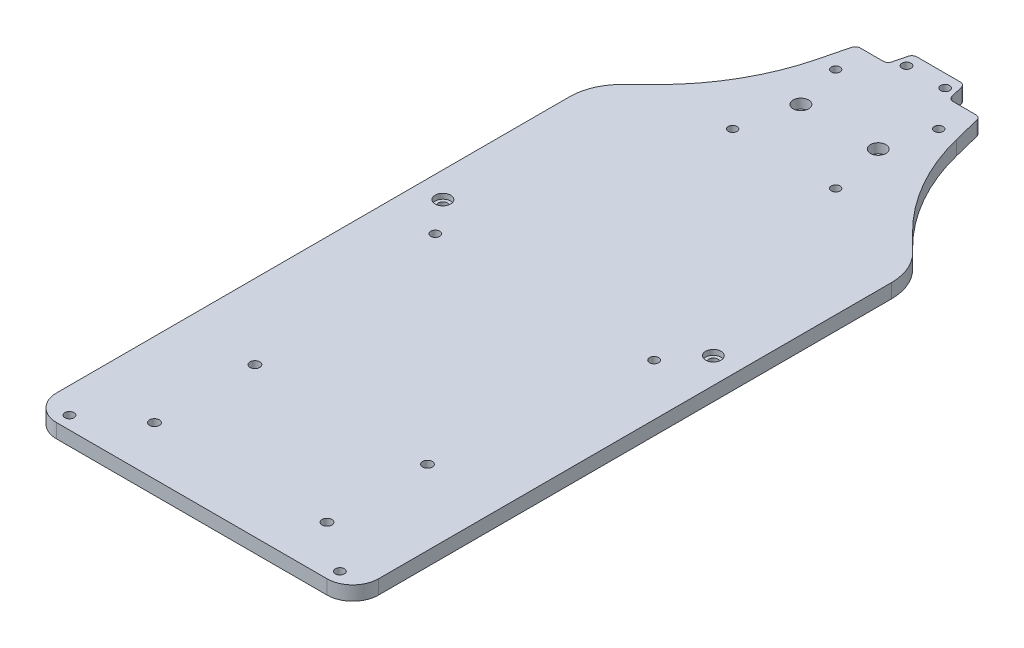
SolidWorks part; units mm, degrees
ref_plane "정면" through (0, 0, 0) normal (0, 0, 1) x (1, 0, 0)
ref_plane "윗면" through (0, 0, 0) normal (0, 1, 0) x (1, 0, 0)
ref_plane "우측면" through (0, 0, 0) normal (1, 0, 0) x (0, 0, -1)
sketch "스케치1" plane through (0, 0, 0) normal (0, 1, 0) x (1, 0, 0)
  line L0 (-857.021, 0) -> (41994.0268, 0) construction
  line L1 (0, -857.021) -> (0, 41994.0268) construction
  line L2 (-72.5, 0) -> (-72.5, -185)
  line L3 (-72.5, 95) -> (72.5, 95) construction
  line L4 (-72.5, 95) -> (-72.5, -195) construction
  line L5 (-72.5, -195) -> (-47.5, -195) construction
  line L6 (72.5, 95) -> (72.5, -195) construction
  line L7 (-62.5, -195) -> (-49.962, -195)
  line L8 (72.5, -185) -> (72.5, 0)
  line L9 (-15.038, -234) -> (15.038, -234)
  line L14 (-19.0011, -232.0486) -> (-45.9989, -196.9514)
  line L15 (-22, 95) -> (22, 95)
  line L16 (-63.6708, 21.2555) -> (-49.4782, 35.3915)
  line L17 (19.0011, -232.0486) -> (45.9989, -196.9514)
  line L18 (857.021, 0) -> (-41994.0268, 0) construction
  line L23 (47.5, -195) -> (72.5, -195) construction
  line L24 (49.962, -195) -> (62.5, -195)
  line L25 (-27, 75) -> (-22, 95)
  line L26 (63.6708, 21.2555) -> (49.4782, 35.3915)
  line L27 (27, 75) -> (22, 95)
  arc A4 (62.5, -195) -> (72.5, -185) centre (62.5, -185) ccw
  arc A5 (-62.5, -195) -> (-72.5, -185) centre (-62.5, -185) cw
  arc A12 (49.962, -195) -> (45.9989, -196.9514) centre (49.962, -200) ccw
  arc A13 (19.0011, -232.0486) -> (15.038, -234) centre (15.038, -229) cw
  arc A14 (-15.038, -234) -> (-19.0011, -232.0486) centre (-15.038, -229) cw
  arc A15 (-49.962, -195) -> (-45.9989, -196.9514) centre (-49.962, -200) cw
  arc A16 (-72.5, 0) -> (-63.6708, 21.2555) centre (-42.5, 0) cw
  arc A17 (-49.4782, 35.3915) -> (-27, 75) centre (-109.4621, 95.6155) ccw
  arc A18 (72.5, 0) -> (63.6708, 21.2555) centre (42.5, 0) ccw
  arc A19 (49.4782, 35.3915) -> (27, 75) centre (109.4621, 95.6155) cw
  point P4 (0, 0)
  point P36 (0, -234)
  point P40 (0, 95)
  point P77 (17.5, -234)
  point P80 (-17.5, -234)
  dimension "D8" = 10
  dimension "D13" = 72.5
  dimension "D14" = 5
  dimension "D17" = 20
  dimension "D15" = 30
  dimension "D16" = 85
  dimension "D1" = 145
  dimension "D2" = 290
  dimension "D3" = 195
  dimension "D9" = 35
  dimension "D10" = 39
  dimension "D11" = 25
  dimension "D12" = 44
  dimension "D18" = 5
extrude "Deck base" add sketch "스케치1" along normal blind 5.5 contours L2 A5 L7 A15 L14 A14 L9 A13 L17 A12 L24 A4 L8 A18 L26 A19 L27 L15 L25 A17 L16 A16
sketch "스케치3" plane through (0, 5.5, 0) normal (0, 1, 0) x (1, 0, 0)
  line L0 (-22, 95) -> (22, 95) construction
  line L1 (0, 0) -> (0, -234) construction
  line L2 (-15.038, -234) -> (15.038, -234) construction
  line L5 (0, -178.2) -> (0, 178.2) construction
  line L6 (0, -200857.021) -> (0, 241994.0268) construction
  circle A0 centre (7.5, 90) radius 1.75
  circle A9 centre (-7.5, 90) radius 1.75
  circle A10 centre (52.5, -45) radius 1.75
  circle A11 centre (52.5, -190) radius 1.75
  circle A14 centre (-52.5, -190) radius 1.75
  circle A15 centre (-52.5, -45) radius 1.75
  dimension "D1" = 3.5
  dimension "D3" = 3.5
  dimension "D8" = 145
  dimension "D9" = 52.5
  dimension "D4" = 3.5
  dimension "D2" = 5
  dimension "D7" = 135
  dimension "D12" = 7.5
extrude "Bolt slot" cut sketch "스케치3" against normal up to next
sketch "스케치14" plane through (0, 5.5, 0) normal (0, 1, 0) x (1, 0, 0)
  circle A0 centre (-52.5, -45) radius 3
  circle A1 centre (52.5, -45) radius 3
  circle A2 centre (-52.5, -45) radius 1.75 construction
  point P6 (0, 0)
  dimension "D1" = 6
  dimension "D4" = 6
extrude "Bolt head" cut sketch "스케치14" against normal blind 2
fillet "필렛1" radius 4 2 edges at (22, 2.75, -95) (-22, 2.75, -95)
sketch "스케치15" plane through (0, 5.5, 0) normal (0, 1, 0) x (1, 0, 0)
  line L0 (72.5, 95) -> (72.5, -195) construction
  line L1 (-72.5, -195) -> (72.5, -195)
  line L2 (-72.5, -195) -> (-72.5, -234)
  line L3 (-72.5, -234) -> (72.5, -234)
  line L4 (72.5, -195) -> (72.5, -234)
  line L5 (-15.038, -234) -> (15.038, -234) construction
extrude "컷-돌출6" cut sketch "스케치15" against normal up to next
sketch "스케치16" plane through (0, 5.5, 0) normal (0, 1, 0) x (1, 0, 0)
  line L0 (-10, 95) -> (10, 95)
  line L1 (-22, 95) -> (22, 95) construction
  line L2 (0, -200857.021) -> (0, 241994.0268) construction
  line L3 (-10, 95) -> (-12, 87)
  line L4 (-12, 87) -> (-24, 87)
  line L5 (-27, 75) -> (-22, 95) construction
  line L6 (10, 95) -> (12, 87)
  line L7 (12, 87) -> (24, 87)
  line L8 (27, 75) -> (22, 95) construction
  line L9 (-24, 87) -> (-24, 100)
  line L10 (-24, 100) -> (24, 100)
  line L11 (24, 100) -> (24, 87)
  point P4 (0, 95)
  dimension "D1" = 20
  dimension "D2" = 8
  dimension "D3" = 5
extrude "컷-돌출7" cut sketch "스케치16" against normal blind 10
fillet "필렛2" radius 2 6 edges at (12, 2.75, -87) (-12, 2.75, -87) (10, 2.75, -95) (-10, 2.75, -95) (24, 2.75, -87) (-24, 2.75, -87)
sketch "스케치17" plane through (0, 5.5, 0) normal (0, 1, 0) x (1, 0, 0)
  line L0 (-72.5, 95) -> (72.5, 95) construction
  line L1 (-62.5, 95) -> (62.5, 95)
  line L2 (-62.5, 95) -> (-62.5, -195)
  line L3 (-62.5, -195) -> (62.5, -195)
  line L4 (62.5, 95) -> (62.5, -195)
  point P7 (0, 0)
extrude "컷-돌출8" cut sketch "스케치17" against normal blind 10 flip side to cut
fillet "필렛4" radius 10 2 edges at (62.5, 2.75, 195) (-62.5, 2.75, 195)
fillet "필렛5" radius 20 2 edges at (62.5, 2.75, -22.4217) (-62.5, 2.75, -22.4217)
sketch "스케치4" plane through (0, 5.5, 0) normal (0, 1, 0) x (1, 0, 0)
  line L0 (-22, 95) -> (22, 95) construction
  line L1 (-20, 75) -> (20, 75) construction
  line L2 (-20, 75) -> (-20, 35) construction
  line L3 (-20, 35) -> (20, 35) construction
  line L4 (20, 75) -> (20, 35) construction
  line L5 (0, -200857.021) -> (0, 241994.0268) construction
  line L6 (0, -178.2) -> (0, 178.2) construction
  circle A0 centre (-20, 75) radius 1.7
  circle A1 centre (-20, 35) radius 1.7
  circle A2 centre (20, 35) radius 1.7
  circle A3 centre (20, 75) radius 1.7
  point P6 (0, 75)
  dimension "D4" = 3.4
  dimension "D5" = 3.4
  dimension "D1" = 40
  dimension "D2" = 40
  dimension "D3" = 20
extrude "Lidar slot" cut sketch "스케치4" against normal up to next
sketch "스케치9" plane through (0, 5.5, 0) normal (0, 1, 0) x (1, 0, 0)
  line L0 (0, -200857.021) -> (0, 241994.0268) construction
  line L1 (-24.5, 80) -> (24.5, 80) construction
  line L2 (-24.5, 80) -> (-24.5, 30) construction
  line L3 (-24.5, 30) -> (-12.5, 30) construction
  line L4 (24.5, 80) -> (24.5, 30) construction
  line L5 (-24.5, 80) -> (24.5, 30) construction
  line L6 (-24.5, 30) -> (24.5, 80) construction
  line L7 (-12.5, 25) -> (12.5, 25) construction
  line L8 (-20, 75) -> (20, 75) construction
  line L9 (12.5, 25) -> (12.5, 30) construction
  line L10 (-12.5, 25) -> (-12.5, 30) construction
  line L11 (12.5, 30) -> (24.5, 30) construction
  point P0 (0, 55)
  point P11 (0, 25)
  dimension "D1" = 49
  dimension "D2" = 50
  dimension "D3" = 5
  dimension "D4" = 25
  dimension "D5" = 5
sketch "스케치6" plane through (0, 5.5, 0) normal (0, 1, 0) x (1, 0, 0)
  line L0 (0, -200857.021) -> (0, 241994.0268) construction
  line L1 (-37, -120) -> (37, -120) construction
  line L2 (-37, -120) -> (-37, -191) construction
  line L3 (-37, -191) -> (37, -191) construction
  line L4 (37, -120) -> (37, -191) construction
  line L6 (0, -3.025) -> (0, 3.025) construction
  line L7 (-12.5, 25) -> (12.5, 25) construction
  circle A0 centre (33.5, -137) radius 1.9
  circle A1 centre (33.5, -176) radius 1.9
  circle A2 centre (-33.5, -176) radius 1.9
  circle A3 centre (-33.5, -137) radius 1.9
  point P4 (0, -120)
  dimension "D3" = 3.8
  dimension "D6" = 3.8
  dimension "D1" = 74
  dimension "D2" = 71
  dimension "D4" = 17
  dimension "D5" = 3.5
  dimension "D7" = 3.5
  dimension "D8" = 15
  dimension "D9" = 145
extrude "Vesc slot" cut sketch "스케치6" against normal up to next
sketch "스케치7" plane through (0, 5.5, 0) normal (0, 1, 0) x (1, 0, 0)
  line L0 (0, -200857.021) -> (0, 241994.0268) construction
  line L1 (-56, 0) -> (56, 0) construction
  line L2 (-56, 0) -> (-56, -116) construction
  line L3 (-56, -116) -> (56, -116) construction
  line L4 (56, 0) -> (56, -116) construction
  line L7 (12.5, 30) -> (24.5, 30) construction
  circle A4 centre (-42.5, -58) radius 1.75
  circle A5 centre (42.5, -58) radius 1.75
  point P4 (0, 0)
  dimension "D6" = 58
  dimension "D7" = 3.5
  dimension "D8" = 3.5
  dimension "D1" = 116
  dimension "D2" = 112
  dimension "D3" = 30
  dimension "D4" = 13.5
  dimension "D5" = 13.5
extrude "Nano slot" cut sketch "스케치7" against normal up to next
sketch "스케치12" plane through (0, 5.5, 0) normal (0, 1, 0) x (1, 0, 0)
  line L0 (-24.5, 30) -> (24.5, 80) construction
  line L1 (-12, 71.5) -> (12, 71.5) construction
  line L2 (-12, 71.5) -> (-12, 38.5) construction
  line L3 (-12, 38.5) -> (12, 38.5) construction
  line L4 (12, 71.5) -> (12, 38.5) construction
  line L5 (-12, 71.5) -> (12, 38.5) construction
  line L6 (-12, 38.5) -> (12, 71.5) construction
  circle A0 centre (-15, 56.5) radius 1.75
  circle A1 centre (15, 56.5) radius 1.75
  point P0 (0, 55)
  dimension "D3" = 3.5
  dimension "D4" = 3.5
  dimension "D1" = 24
  dimension "D2" = 33
  dimension "D5" = 15
  dimension "D6" = 15
  dimension "D7" = 15
extrude "컷-돌출3" cut sketch "스케치12" against normal up to next
sketch "스케치13" plane through (0, 5.5, 0) normal (0, 1, 0) x (1, 0, 0)
  circle A0 centre (-15, 56.5) radius 3
  circle A1 centre (15, 56.5) radius 3
  dimension "D1" = 6
  dimension "D2" = 6
extrude "컷-돌출4" cut sketch "스케치13" against normal blind 3.7
